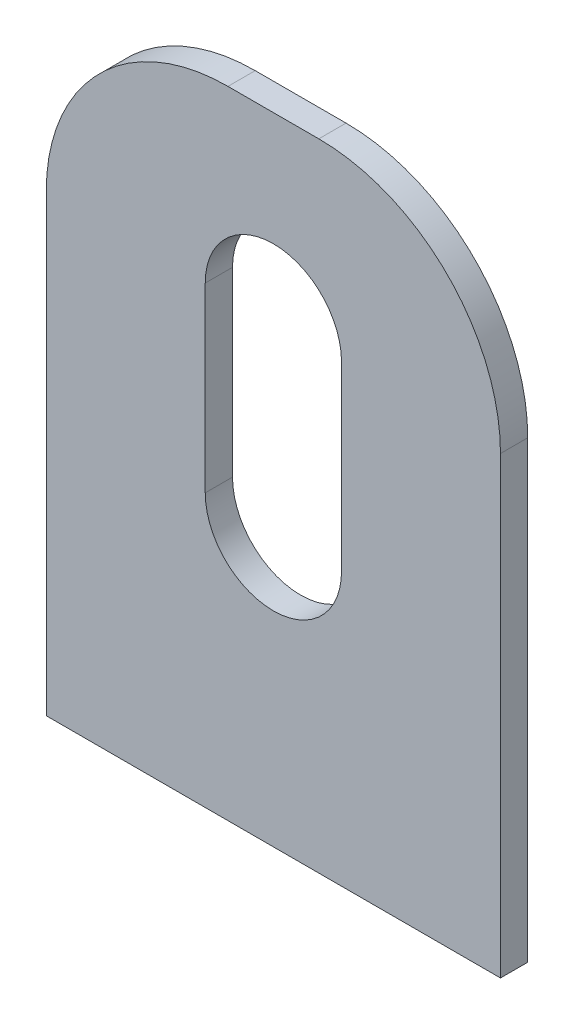
SolidWorks part; units mm, degrees
ref_plane "Front Plane" through (0, 0, 0) normal (0, 0, 1) x (1, 0, 0)
ref_plane "Top Plane" through (0, 0, 0) normal (0, 1, 0) x (1, 0, 0)
ref_plane "Right Plane" through (0, 0, 0) normal (1, 0, 0) x (0, 0, -1)
sketch "Sketch1" plane through (0, 0, 0) normal (0, 0, 1) x (1, 0, 0)
  line L1 (-25, 40) -> (25, 40)
  line L2 (-25, 40) -> (-25, -30)
  line L3 (-25, -30) -> (25, -30)
  line L4 (25, 40) -> (25, -30)
  point P4 (-29.8291, 41.9051)
  point P6 (29.9926, 45.6966)
  point P7 (0, 0)
  point P8 (0, -30)
  dimension "D1" = 30
  dimension "D2" = 50
  dimension "D3" = 40
extrude "Boss-Extrude1" add sketch "Sketch1" along normal blind 3
sketch "Sketch2" plane through (0, 0, 3) normal (0, 0, 1) x (1, 0, 0)
  line L0 (0, 0) -> (0, 20) construction
  line L1 (-7.5, 0) -> (-7.5, 20)
  line L2 (7.5, 0) -> (7.5, 20)
  arc A1 (-7.5, 0) -> (7.5, 0) centre (0, 0) ccw
  arc A2 (7.5, 20) -> (-7.5, 20) centre (0, 20) ccw
  point P4 (0, 10)
  dimension "D1" = 7.5
  dimension "D2" = 20
extrude "Cut-Extrude1" cut sketch "Sketch2" against normal through all both and the other way through all
fillet "Fillet1" radius 20 2 edges at (25, 40, 1.5) (-25, 40, 1.5)
